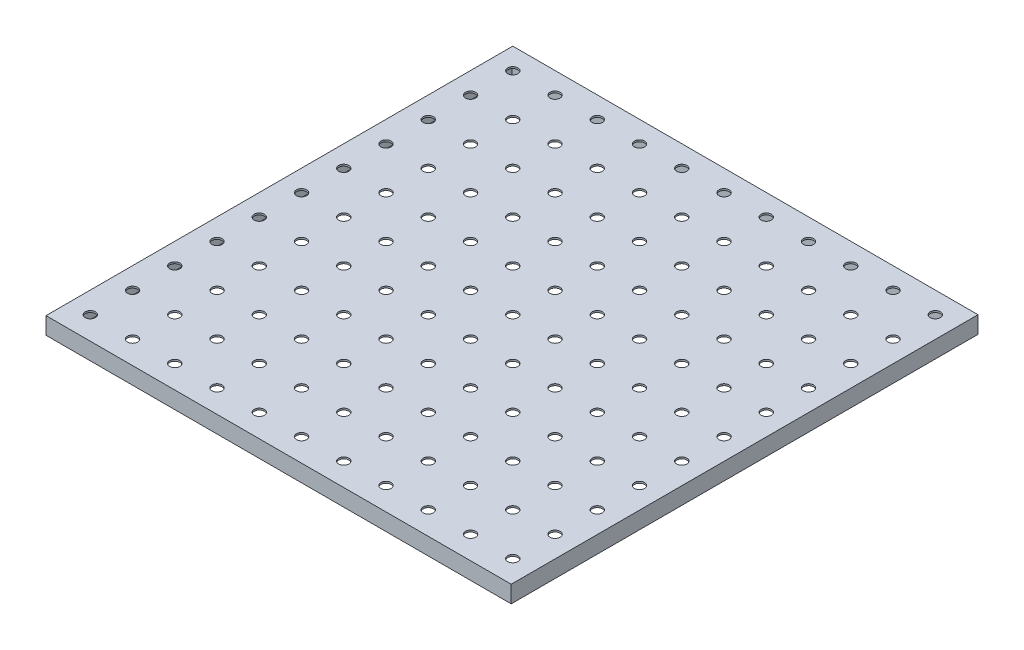
SolidWorks part; units mm, degrees
ref_plane "Front Plane" through (0, 0, 0) normal (0, 0, 1) x (1, 0, 0)
ref_plane "Top Plane" through (0, 0, 0) normal (0, 1, 0) x (1, 0, 0)
ref_plane "Right Plane" through (0, 0, 0) normal (1, 0, 0) x (0, 0, -1)
sketch "Sketch1" plane through (0, 0, 0) normal (0, 1, 0) x (1, 0, 0)
  line L5 (-136.5357, -136.9984) -> (136.5357, -136.9984)
  line L6 (-136.5357, -136.9984) -> (-136.5357, 136.9984)
  line L7 (-136.5357, 136.9984) -> (136.5357, 136.9984)
  line L8 (136.5357, -136.9984) -> (136.5357, 136.9984)
  circle A146 centre (-124.0007, 124.4634) radius 3
  circle A147 centre (-99.2007, 124.4634) radius 3
  circle A148 centre (-74.4007, 124.4634) radius 3
  circle A149 centre (-49.6007, 124.4634) radius 3
  circle A150 centre (-24.8007, 124.4634) radius 3
  circle A151 centre (-0.0007, 124.4634) radius 3
  circle A152 centre (24.7993, 124.4634) radius 3
  circle A153 centre (49.5993, 124.4634) radius 3
  circle A154 centre (74.3993, 124.4634) radius 3
  circle A155 centre (99.1993, 124.4634) radius 3
  circle A156 centre (123.9993, 124.4634) radius 3
  circle A157 centre (-99.2007, 99.6634) radius 3
  circle A158 centre (-74.4007, 99.6634) radius 3
  circle A159 centre (-49.6007, 99.6634) radius 3
  circle A160 centre (-24.8007, 99.6634) radius 3
  circle A161 centre (-0.0007, 99.6634) radius 3
  circle A162 centre (24.7993, 99.6634) radius 3
  circle A163 centre (49.5993, 99.6634) radius 3
  circle A164 centre (74.3993, 99.6634) radius 3
  circle A165 centre (99.1993, 99.6634) radius 3
  circle A166 centre (123.9993, 99.6634) radius 3
  circle A167 centre (-99.2007, 74.8634) radius 3
  circle A168 centre (-74.4007, 74.8634) radius 3
  circle A169 centre (-49.6007, 74.8634) radius 3
  circle A170 centre (-24.8007, 74.8634) radius 3
  circle A171 centre (-0.0007, 74.8634) radius 3
  circle A172 centre (24.7993, 74.8634) radius 3
  circle A173 centre (49.5993, 74.8634) radius 3
  circle A174 centre (74.3993, 74.8634) radius 3
  circle A175 centre (99.1993, 74.8634) radius 3
  circle A176 centre (123.9993, 74.8634) radius 3
  circle A177 centre (-99.2007, 50.0634) radius 3
  circle A178 centre (-74.4007, 50.0634) radius 3
  circle A179 centre (-49.6007, 50.0634) radius 3
  circle A180 centre (-24.8007, 50.0634) radius 3
  circle A181 centre (-0.0007, 50.0634) radius 3
  circle A182 centre (24.7993, 50.0634) radius 3
  circle A183 centre (49.5993, 50.0634) radius 3
  circle A184 centre (74.3993, 50.0634) radius 3
  circle A185 centre (99.1993, 50.0634) radius 3
  circle A186 centre (123.9993, 50.0634) radius 3
  circle A187 centre (-99.2007, 25.2634) radius 3
  circle A188 centre (-74.4007, 25.2634) radius 3
  circle A189 centre (-49.6007, 25.2634) radius 3
  circle A190 centre (-24.8007, 25.2634) radius 3
  circle A191 centre (-0.0007, 25.2634) radius 3
  circle A192 centre (24.7993, 25.2634) radius 3
  circle A193 centre (49.5993, 25.2634) radius 3
  circle A194 centre (74.3993, 25.2634) radius 3
  circle A195 centre (99.1993, 25.2634) radius 3
  circle A196 centre (123.9993, 25.2634) radius 3
  circle A197 centre (-99.2007, 0.4634) radius 3
  circle A198 centre (-74.4007, 0.4634) radius 3
  circle A199 centre (-49.6007, 0.4634) radius 3
  circle A200 centre (-24.8007, 0.4634) radius 3
  circle A201 centre (-0.0007, 0.4634) radius 3
  circle A202 centre (24.7993, 0.4634) radius 3
  circle A203 centre (49.5993, 0.4634) radius 3
  circle A204 centre (74.3993, 0.4634) radius 3
  circle A205 centre (99.1993, 0.4634) radius 3
  circle A206 centre (123.9993, 0.4634) radius 3
  circle A207 centre (-99.2007, -24.3366) radius 3
  circle A208 centre (-74.4007, -24.3366) radius 3
  circle A209 centre (-49.6007, -24.3366) radius 3
  circle A210 centre (-24.8007, -24.3366) radius 3
  circle A211 centre (-0.0007, -24.3366) radius 3
  circle A212 centre (24.7993, -24.3366) radius 3
  circle A213 centre (49.5993, -24.3366) radius 3
  circle A214 centre (74.3993, -24.3366) radius 3
  circle A215 centre (99.1993, -24.3366) radius 3
  circle A216 centre (123.9993, -24.3366) radius 3
  circle A217 centre (-99.2007, -49.1366) radius 3
  circle A218 centre (-74.4007, -49.1366) radius 3
  circle A219 centre (-49.6007, -49.1366) radius 3
  circle A220 centre (-24.8007, -49.1366) radius 3
  circle A221 centre (-0.0007, -49.1366) radius 3
  circle A222 centre (24.7993, -49.1366) radius 3
  circle A223 centre (49.5993, -49.1366) radius 3
  circle A224 centre (74.3993, -49.1366) radius 3
  circle A225 centre (99.1993, -49.1366) radius 3
  circle A226 centre (123.9993, -49.1366) radius 3
  circle A227 centre (-99.2007, -73.9366) radius 3
  circle A228 centre (-74.4007, -73.9366) radius 3
  circle A229 centre (-49.6007, -73.9366) radius 3
  circle A230 centre (-24.8007, -73.9366) radius 3
  circle A231 centre (-0.0007, -73.9366) radius 3
  circle A232 centre (24.7993, -73.9366) radius 3
  circle A233 centre (49.5993, -73.9366) radius 3
  circle A234 centre (74.3993, -73.9366) radius 3
  circle A235 centre (99.1993, -73.9366) radius 3
  circle A236 centre (123.9993, -73.9366) radius 3
  circle A237 centre (-99.2007, -98.7366) radius 3
  circle A238 centre (-74.4007, -98.7366) radius 3
  circle A239 centre (-49.6007, -98.7366) radius 3
  circle A240 centre (-24.8007, -98.7366) radius 3
  circle A241 centre (-0.0007, -98.7366) radius 3
  circle A242 centre (24.7993, -98.7366) radius 3
  circle A243 centre (49.5993, -98.7366) radius 3
  circle A244 centre (74.3993, -98.7366) radius 3
  circle A245 centre (99.1993, -98.7366) radius 3
  circle A246 centre (123.9993, -98.7366) radius 3
  circle A247 centre (-99.2007, -123.5366) radius 3
  circle A248 centre (-74.4007, -123.5366) radius 3
  circle A249 centre (-49.6007, -123.5366) radius 3
  circle A250 centre (-24.8007, -123.5366) radius 3
  circle A251 centre (-0.0007, -123.5366) radius 3
  circle A252 centre (24.7993, -123.5366) radius 3
  circle A253 centre (49.5993, -123.5366) radius 3
  circle A254 centre (74.3993, -123.5366) radius 3
  circle A255 centre (99.1993, -123.5366) radius 3
  circle A256 centre (123.9993, -123.5366) radius 3
  circle A257 centre (-124.0007, 99.6634) radius 3
  circle A258 centre (-124.0007, 74.8634) radius 3
  circle A259 centre (-124.0007, 50.0634) radius 3
  circle A260 centre (-124.0007, 25.2634) radius 3
  circle A261 centre (-124.0007, 0.4634) radius 3
  circle A262 centre (-124.0007, -24.3366) radius 3
  circle A263 centre (-124.0007, -49.1366) radius 3
  circle A264 centre (-124.0007, -73.9366) radius 3
  circle A265 centre (-124.0007, -98.7366) radius 3
  circle A266 centre (-124.0007, -123.5366) radius 3
  point P0 (0, 0)
  dimension "D1" = 6
  dimension "D2" = 11
  dimension "D3" = 11
  dimension "D4" = 12.535
  dimension "D5" = 12.535
extrude "Boss-Extrude1" add sketch "Sketch1" along normal blind 10
sketch "Sketch2" plane through (0, 0, 0) normal (0, -1, 0) x (1, 0, 0)
  line L0 (-136.5357, -136.9984) -> (-136.5357, 136.9984) construction
  line L1 (131.5357, 131.5357) -> (-131.5357, 131.5357)
  line L2 (131.5357, 131.5357) -> (131.5357, -131.5357)
  line L3 (131.5357, -131.5357) -> (-131.5357, -131.5357)
  line L4 (-131.5357, 131.5357) -> (-131.5357, -131.5357)
  line L5 (131.5357, 131.5357) -> (-131.5357, -131.5357) construction
  line L6 (131.5357, -131.5357) -> (-131.5357, 131.5357) construction
  point P0 (0, 0)
  dimension "D1" = 5
extrude "Cut-Extrude1" cut sketch "Sketch2" against normal blind 9
